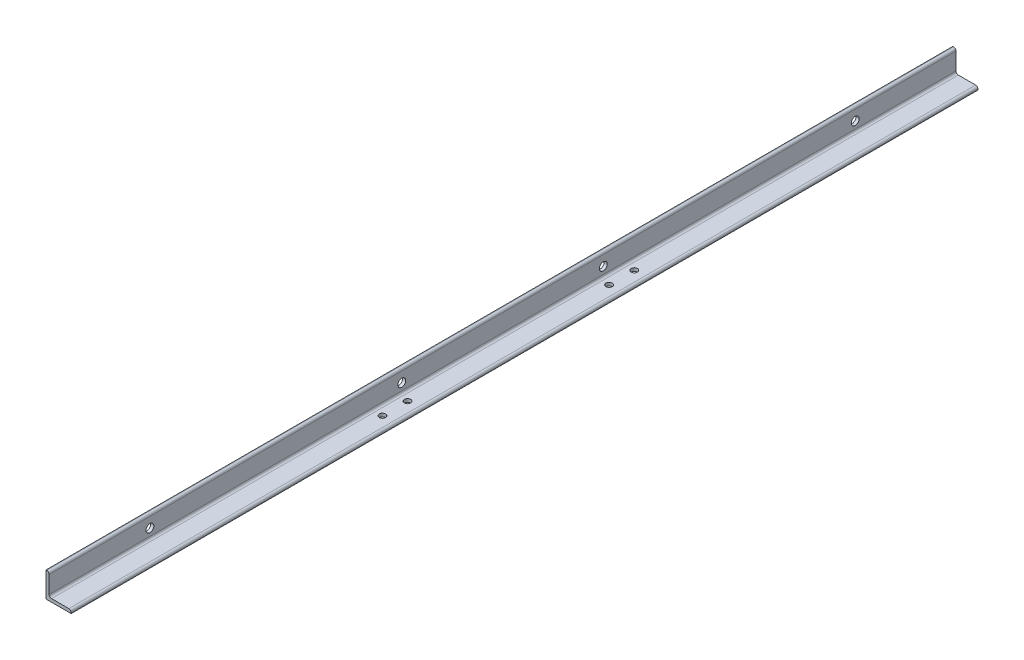
SolidWorks part; units mm, degrees
ref_plane "Front Plane" through (0, 0, 0) normal (0, 0, 1) x (1, 0, 0)
ref_plane "Top Plane" through (0, 0, 0) normal (0, 1, 0) x (1, 0, 0)
ref_plane "Right Plane" through (0, 0, 0) normal (1, 0, 0) x (0, 0, -1)
sketch "Sketch1" plane through (0, 0, 0) normal (0, 0, 1) x (1, 0, 0)
  line L0 (0, 0) -> (0, 50.8)
  line L1 (0, 50.8) -> (1.5926, 50.8)
  line L2 (6.35, 46.0426) -> (6.35, 11.1125)
  line L3 (11.1125, 6.35) -> (46.0426, 6.35)
  line L4 (50.8, 1.5926) -> (50.8, 0)
  line L5 (50.8, 0) -> (0, 0)
  arc A0 (50.8, 1.5926) -> (46.0426, 6.35) centre (46.0426, 1.5926) ccw
  arc A1 (1.5926, 50.8) -> (6.35, 46.0426) centre (1.5926, 46.0426) cw
  arc A2 (11.1125, 6.35) -> (6.35, 11.1125) centre (11.1125, 11.1125) cw
  circle A3 centre (0, 0) radius 4.7625 construction
  dimension "D2" = 1.5926
  dimension "Radius_1" = 4.7625
  dimension "Radius_2" = 4.7625
  dimension "D1" = 6.35
  dimension "V_leg" = 50.8
  dimension "H_leg" = 50.8
  dimension "Thickness" = 6.35
  dimension "Flat_wid" = 1.5926
extrude "Boss-Extrude1" add sketch "Sketch1" along normal mid plane 1828.8
hole_wizard "13/16 (0.8125) Diameter Hole1" positions "Sketch4" profile "Sketch3" hole size "13/16" standard "Ansi Inch" end condition up to next
sketch "Sketch4" plane through (0, 0, 0) normal (0, -1, 0) x (1, 0, 0)
  line L2 (25.4, -914.4) -> (25.4, 914.4) construction
  line L3 (0, 914.4) -> (50.8, 914.4) construction
  line L4 (0, -914.4) -> (50.8, -914.4) construction
  circle A0 centre (25.4, -246.634) radius 6.35
  circle A2 centre (25.4, 261.366) radius 6.35
  point P0 (25.4, -195.834)
  point P1 (25.4, 210.566)
  dimension "D3" = 50.8
  dimension "D4" = 50.8
  dimension "D1" = 718.566
  dimension "D2" = 703.834
sketch "Sketch3" plane through (25.4, 0, -195.834) normal (1, 0, 0) x (0, 0, -1)
  line L0 (0, 0) -> (0, 6.35)
  line L1 (0, 6.35) -> (6.35, 6.35)
  line L2 (6.35, 6.35) -> (6.35, 0)
  line L5 (6.35, 0) -> (0, 0)
  line L11 (0, -6.35) -> (0, 107.95) construction
  dimension "Thru Hole Dia." = 12.7
  dimension "Thru Hole Depth" = 6.35
hole_wizard "5/8 (0.625) Diameter Hole1" positions "Sketch6" profile "Sketch5" hole size "5/8" standard "Ansi Inch" end condition up to next
sketch "Sketch6" plane through (0, 0, 0) normal (-1, 0, 0) x (0, 0, 1)
  line L0 (-914.4, 25.4) -> (914.4, 25.4) construction
  line L3 (-914.4, 50.8) -> (-914.4, 0) construction
  line L4 (914.4, 50.8) -> (914.4, 0) construction
  point P0 (-711.2, 25.4)
  point P1 (-203.2, 25.4)
  point P3 (203.2, 25.4)
  point P5 (711.2, 25.4)
  dimension "D1" = 508
  dimension "D2" = 508
  dimension "D3" = 203.2
  dimension "D4" = 406.4
sketch "Sketch5" plane through (0, 25.4, -711.2) normal (0, 1, 0) x (0, 0, 1)
  line L0 (0, 0) -> (0, 6.35)
  line L1 (0, 6.35) -> (7.9375, 6.35)
  line L2 (7.9375, 6.35) -> (7.9375, 0)
  line L5 (7.9375, 0) -> (0, 0)
  line L11 (0, -6.35) -> (0, 107.95) construction
  dimension "Thru Hole Dia." = 15.875
  dimension "Thru Hole Depth" = 6.35
sketch "Sketch7" plane through (0, 6.35, 0) normal (0, 1, 0) x (1, 0, 0)
  line L0 (27.6093, 873.8043) -> (27.6093, -957.2792) construction
  line L1 (25.4, 202.184) -> (25.4, 914.4) construction
  line L2 (46.0426, 914.4) -> (11.1125, 914.4) construction
  line L3 (25.4, 914.4) -> (25.4, -914.4) construction
  line L4 (46.0426, -914.4) -> (11.1125, -914.4) construction
  circle A0 centre (25.4, 195.834) radius 6.35 construction
  circle A1 centre (25.4, 246.634) radius 6.35
  circle A2 centre (25.4, -261.366) radius 6.35
  circle A5 centre (25.4, -210.566) radius 6.35 construction
  dimension "D1" = 50.8
  dimension "D2" = 50.8
extrude "Cut-Extrude1" cut sketch "Sketch7" against normal through all
